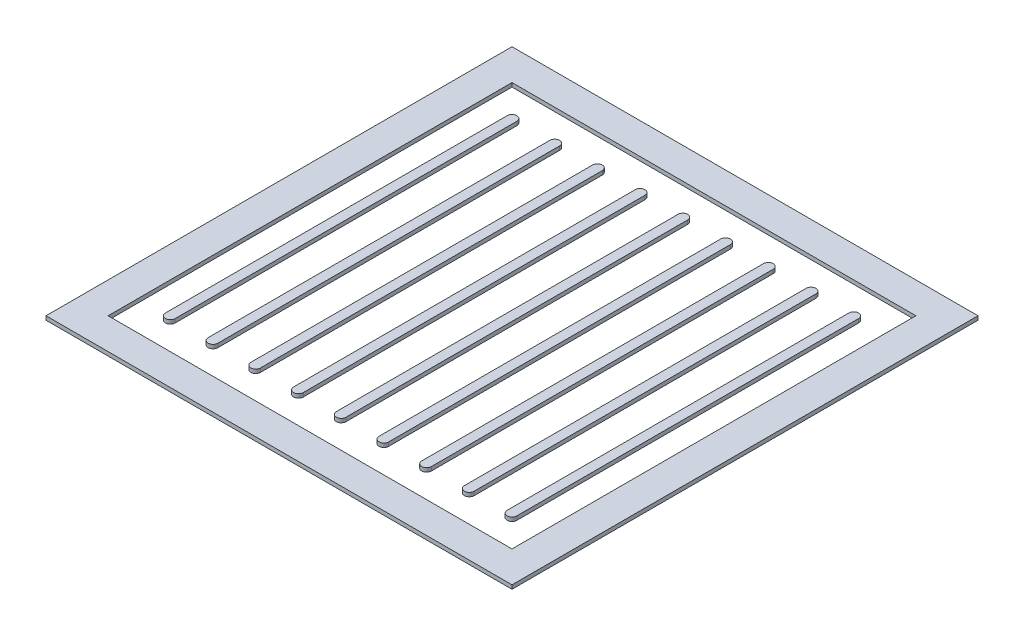
SolidWorks part; units mm, degrees
ref_plane "Front Plane" through (0, 0, 0) normal (0, 0, 1) x (1, 0, 0)
ref_plane "Top Plane" through (0, 0, 0) normal (0, 1, 0) x (1, 0, 0)
ref_plane "Right Plane" through (0, 0, 0) normal (1, 0, 0) x (0, 0, -1)
sketch "Sketch1" plane through (0, 0, 0) normal (0, 1, 0) x (1, 0, 0)
  line L0 (-139.7, 139.7) -> (-139.7, -139.7) construction
  line L1 (-190.5, -190.5) -> (190.5, -190.5)
  line L2 (-190.5, -190.5) -> (-190.5, 190.5)
  line L3 (-190.5, 190.5) -> (190.5, 190.5)
  line L4 (190.5, -190.5) -> (190.5, 190.5)
  line L5 (-190.5, -190.5) -> (190.5, 190.5) construction
  line L6 (-190.5, 190.5) -> (190.5, -190.5) construction
  line L7 (-165.1, -165.1) -> (165.1, -165.1)
  line L8 (-165.1, -165.1) -> (-165.1, 165.1)
  line L9 (-165.1, 165.1) -> (165.1, 165.1)
  line L10 (165.1, -165.1) -> (165.1, 165.1)
  line L11 (-165.1, -165.1) -> (165.1, 165.1) construction
  line L12 (-165.1, 165.1) -> (165.1, -165.1) construction
  line L13 (-135.7312, 139.7) -> (-135.7312, -139.7)
  line L14 (-143.6687, 139.7) -> (-143.6687, -139.7)
  line L15 (139.7, 139.7) -> (139.7, -139.7) construction
  line L16 (143.6687, 139.7) -> (143.6688, -139.7)
  line L17 (135.7312, 139.7) -> (135.7313, -139.7)
  line L18 (-139.7, 139.7) -> (139.7, 139.7) construction
  line L19 (-104.775, 139.7) -> (-104.775, -139.7) construction
  line L20 (-100.8062, 139.7) -> (-100.8062, -139.7)
  line L21 (-108.7438, 139.7) -> (-108.7438, -139.7)
  line L22 (-69.85, 139.7) -> (-69.85, -139.7) construction
  line L23 (-65.8812, 139.7) -> (-65.8812, -139.7)
  line L24 (-73.8188, 139.7) -> (-73.8188, -139.7)
  line L25 (-34.925, 139.7) -> (-34.925, -139.7) construction
  line L26 (-30.9562, 139.7) -> (-30.9562, -139.7)
  line L27 (-38.8938, 139.7) -> (-38.8938, -139.7)
  line L28 (0, 139.7) -> (0, -139.7) construction
  line L29 (3.9688, 139.7) -> (3.9688, -139.7)
  line L30 (-3.9688, 139.7) -> (-3.9688, -139.7)
  line L31 (34.925, 139.7) -> (34.925, -139.7) construction
  line L32 (38.8938, 139.7) -> (38.8938, -139.7)
  line L33 (30.9562, 139.7) -> (30.9562, -139.7)
  line L34 (69.85, 139.7) -> (69.85, -139.7) construction
  line L35 (73.8188, 139.7) -> (73.8188, -139.7)
  line L36 (65.8813, 139.7) -> (65.8813, -139.7)
  line L37 (104.775, 139.7) -> (104.775, -139.7) construction
  line L38 (108.7438, 139.7) -> (108.7438, -139.7)
  line L39 (100.8062, 139.7) -> (100.8062, -139.7)
  line L40 (69.85, 41.3413) -> (139.7, 41.3413) construction
  arc A0 (-135.7312, 139.7) -> (-143.6687, 139.7) centre (-139.7, 139.7) ccw
  arc A1 (-143.6687, -139.7) -> (-135.7312, -139.7) centre (-139.7, -139.7) ccw
  arc A2 (143.6687, 139.7) -> (135.7312, 139.7) centre (139.7, 139.7) ccw
  arc A3 (135.7313, -139.7) -> (143.6688, -139.7) centre (139.7, -139.7) ccw
  arc A4 (-100.8062, 139.7) -> (-108.7438, 139.7) centre (-104.775, 139.7) ccw
  arc A5 (-108.7438, -139.7) -> (-100.8062, -139.7) centre (-104.775, -139.7) ccw
  arc A6 (-65.8812, 139.7) -> (-73.8188, 139.7) centre (-69.85, 139.7) ccw
  arc A7 (-73.8188, -139.7) -> (-65.8812, -139.7) centre (-69.85, -139.7) ccw
  arc A8 (-30.9562, 139.7) -> (-38.8938, 139.7) centre (-34.925, 139.7) ccw
  arc A9 (-38.8938, -139.7) -> (-30.9562, -139.7) centre (-34.925, -139.7) ccw
  arc A10 (3.9688, 139.7) -> (-3.9688, 139.7) centre (0, 139.7) ccw
  arc A11 (-3.9688, -139.7) -> (3.9688, -139.7) centre (0, -139.7) ccw
  arc A12 (38.8938, 139.7) -> (30.9562, 139.7) centre (34.925, 139.7) ccw
  arc A13 (30.9562, -139.7) -> (38.8938, -139.7) centre (34.925, -139.7) ccw
  arc A14 (73.8188, 139.7) -> (65.8813, 139.7) centre (69.85, 139.7) ccw
  arc A15 (65.8813, -139.7) -> (73.8188, -139.7) centre (69.85, -139.7) ccw
  arc A16 (108.7438, 139.7) -> (100.8062, 139.7) centre (104.775, 139.7) ccw
  arc A17 (100.8062, -139.7) -> (108.7438, -139.7) centre (104.775, -139.7) ccw
  point P0 (0, 0)
  point P6 (0, 0)
  point P13 (-139.7, 0)
  point P18 (139.7, 0)
  point P27 (104.775, 41.3413)
  point P30 (-104.775, 0)
  point P37 (-69.85, 0)
  point P44 (-34.925, 0)
  point P51 (0, 0)
  point P58 (34.925, 0)
  point P65 (69.85, 0)
  point P72 (104.775, 0)
  dimension "D1" = 381
  dimension "D2" = 25.4
  dimension "D3" = 7.9375
  dimension "D4" = 25.4
  dimension "D5" = 8
extrude "Boss-Extrude1" add sketch "Sketch1" along normal blind 3.175 contours L1 L4 L3 L2 L10 L7 L8 L9 | L39 A17 L38 A16 | L17 A3 L16 A2 | L36 A15 L35 A14 | L33 A13 L32 A12 | L30 A11 L29 A10 | L24 A7 L23 A6 | L27 A9 L26 A8 | L21 A5 L20 A4 | L14 A1 L13 A0
